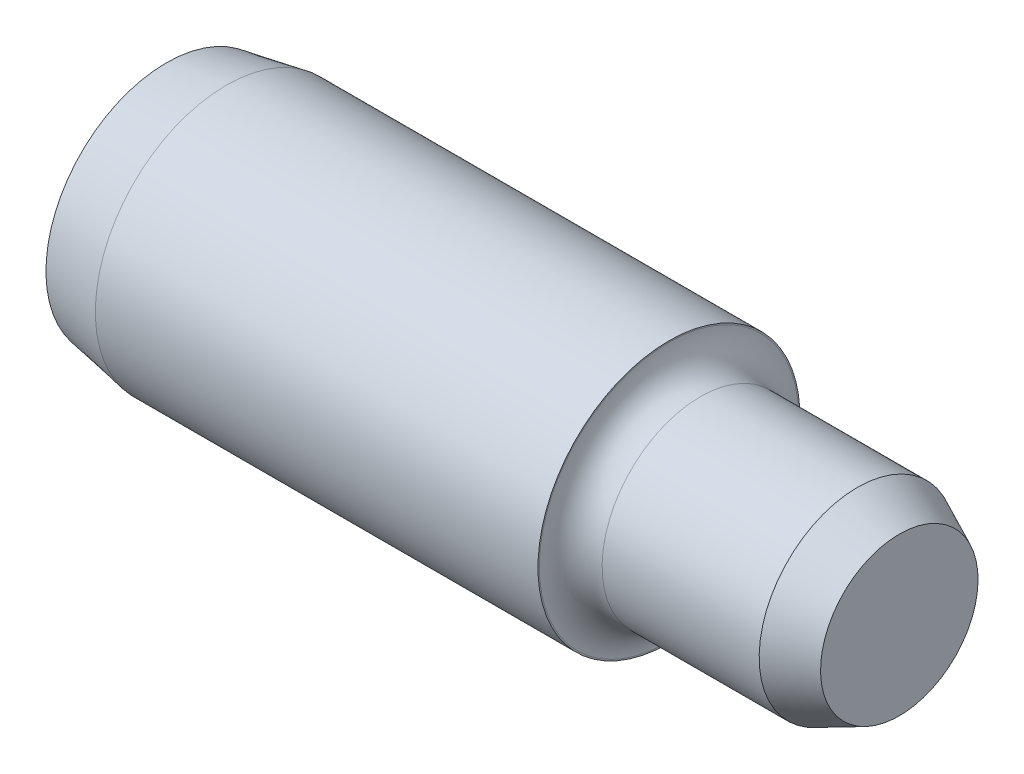
SolidWorks part; units mm, degrees
material "304, 316 OR 302 SSTL"
ref_plane "Front Plane" through (0, 0, 0) normal (0, 0, 1) x (1, 0, 0)
ref_plane "Top Plane" through (0, 0, 0) normal (0, 1, 0) x (1, 0, 0)
ref_plane "Right Plane" through (0, 0, 0) normal (1, 0, 0) x (0, 0, -1)
sketch "Sketch1" plane through (0, 0, 0) normal (0, 0, 1) x (1, 0, 0)
  line L7 (12.192, -3.1775) -> (12.192, -3.1458)
  line L8 (0, 0) -> (0, -2.921)
  line L9 (1.4549, -3.1775) -> (12.192, -3.1775)
  line L11 (0, 0) -> (8.89, 0)
  line L12 (0, -2.921) -> (1.4549, -3.1775)
  line L13 (17.78, 0) -> (17.78, -1.91)
  line L14 (17.78, -1.91) -> (16.764, -2.3838)
  line L15 (0, 0) -> (-2.921, 0) construction
  line L16 (8.89, 0) -> (17.78, 0)
  line L17 (12.954, -2.3838) -> (16.764, -2.3838)
  arc A0 (12.192, -3.1458) -> (12.954, -2.3838) centre (12.954, -3.1458) cw
  dimension "D3" = 10
  dimension "D4" = 1.016
  dimension "D8" = 5.588
  dimension "D1" = 4.7676
  dimension "D5" = 25
  dimension "D9" = 5.842
  dimension "D10" = 0.762
  dimension "D2" = 17.78
  dimension "D6" = 10.7371
  dimension "D7" = 6.3551
  dimension "D11" = 4.826
  dimension "D12" = 12.192
revolve "Revolve1" add sketch "Sketch1" angle 360 about L15
